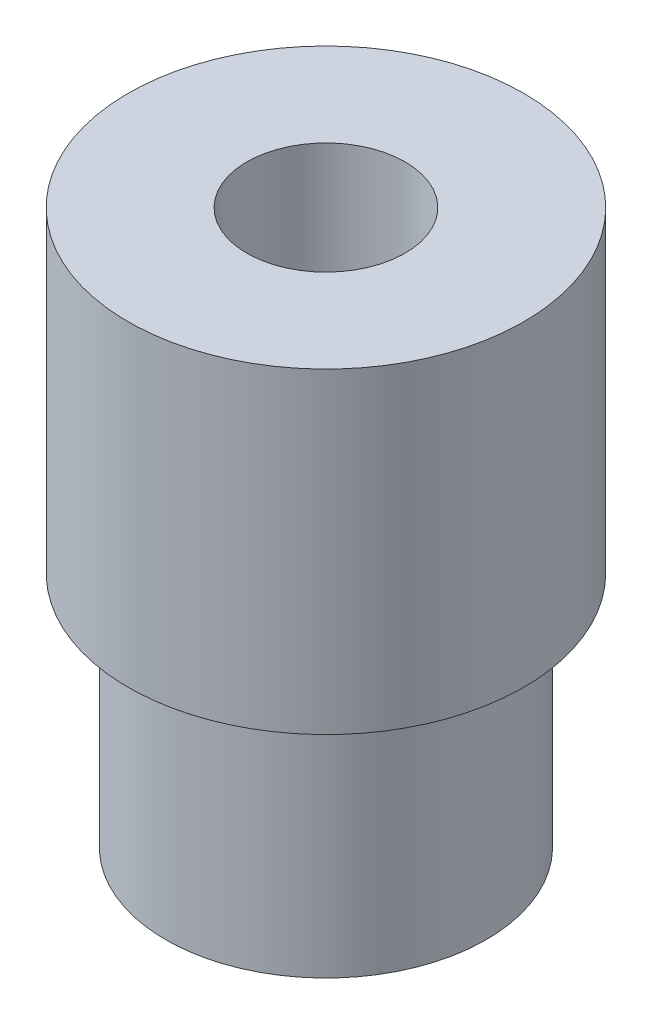
SolidWorks part; units mm, degrees
ref_plane "Front" through (0, 0, 0) normal (0, 0, 1) x (1, 0, 0)
ref_plane "Top" through (0, 0, 0) normal (0, 1, 0) x (1, 0, 0)
ref_plane "Right" through (0, 0, 0) normal (1, 0, 0) x (0, 0, -1)
sketch "Esquisse1" plane through (0, 0, 0) normal (0, 0, 1) x (1, 0, 0)
  line L0 (0, 0) -> (0, 25.3714) construction
  line L1 (2, 14) -> (5, 14)
  line L2 (5, 14) -> (5, 6)
  line L3 (5, 6) -> (4.05, 6)
  line L4 (4.05, 6) -> (4.05, 0)
  line L5 (4.05, 0) -> (2, 0)
  line L6 (2, 0) -> (0, 0) construction
  line L8 (2, 0) -> (2, 14)
  dimension "D1" = 14
  dimension "D2" = 10
  dimension "D3" = 8.1
  dimension "D6" = 8
  dimension "D7" = 4
revolve "Révolution1" add sketch "Esquisse1" angle 360 about L0
